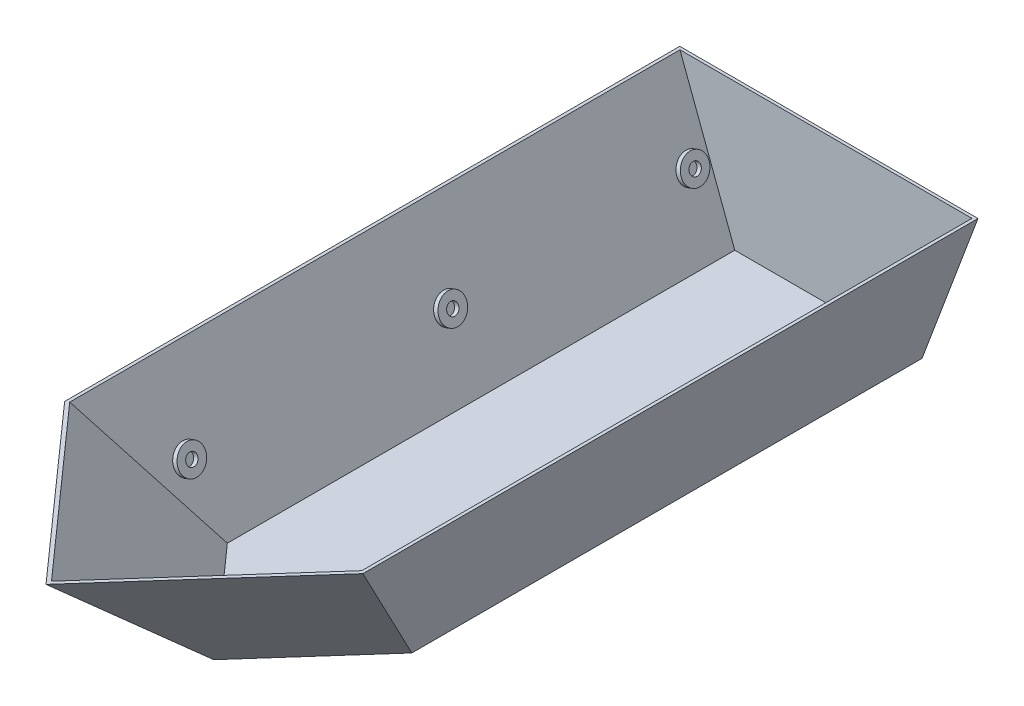
SolidWorks part; units mm, degrees
ref_plane "Front Plane" through (0, 0, 0) normal (0, 0, 1) x (1, 0, 0)
ref_plane "Top Plane" through (0, 0, 0) normal (0, 1, 0) x (1, 0, 0)
ref_plane "Right Plane" through (0, 0, 0) normal (1, 0, 0) x (0, 0, -1)
sketch "Sketch1" plane through (0, 0, 0) normal (0, 0, 1) x (1, 0, 0)
  line L0 (0, 0) -> (508, 0)
  line L1 (0, 0) -> (0, 406.4) construction
  line L2 (0, 406.4) -> (-152.4, 406.4) construction
  line L3 (-152.4, 406.4) -> (0, 0)
  line L4 (508, 0) -> (660.4, 0) construction
  line L5 (508, 0) -> (660.4, 406.4)
  line L6 (660.4, 406.4) -> (-152.4, 406.4)
  line L7 (660.4, 0) -> (660.4, 406.4) construction
  dimension "D1" = 508
  dimension "D2" = 406.4
  dimension "D3" = 152.4
  dimension "D4" = 152.4
extrude "Boss-Extrude1" add sketch "Sketch1" along normal blind 2133.6
sketch "Sketch4" plane through (0, 406.4, 0) normal (0, 1, 0) x (1, 0, 0)
  line L4 (660.4, -2133.6) -> (660.4, -1676.4) construction
  line L5 (660.4, -2133.6) -> (660.4, 0) construction
  line L6 (660.4, -1676.4) -> (-152.4, -1676.4) construction
  line L7 (-152.4, -2133.6) -> (-152.4, 0) construction
  line L11 (-152.4, -1676.4) -> (254, -2133.6) construction
  line L12 (660.4, -2133.6) -> (-152.4, -2133.6) construction
  line L13 (254, -2133.6) -> (660.4, -1676.4) construction
  dimension "D1" = 457.2
ref_plane "Plane2" through (254, 0, 0) normal (1, 0, 0) x (0, 0, -1)
sketch "Sketch13" plane through (254, 0, 0) normal (1, 0, 0) x (0, 0, -1)
  line L0 (-2133.6, 0) -> (-3174.6486, 0)
  line L1 (-2133.6, 406.4) -> (-1676.4, 0)
  line L2 (-2133.6, 406.4) -> (-1676.4, 406.4) construction
  line L3 (-2133.6, 0) -> (0, 0) construction
  line L5 (-2133.6, 0) -> (-1676.4, 0)
  line L6 (-3174.6486, 0) -> (-3174.6486, 406.4)
  line L7 (-3174.6486, 406.4) -> (-2133.6, 406.4)
  dimension "D1" = 457.2
extrude "Cut-Extrude2" cut sketch "Sketch13" along direction (0.6644, 0, 0.7474) on the side against the normal through all and the other way through all contours L7 L1 L5 L0 L6
mirror "Mirror1" about plane through (254, 0, 0) normal (1, 0, 0) of "Cut-Extrude2"
shell "Shell1" thickness 7.9375
sketch "Sketch14" plane through (437.9378, -164.2267, 0) normal (-0.9363, 0.3511, 0) x (0, 0, 1)
  line L1 (7.9375, 183.8714) -> (7.9375, 609.4295) construction
  line L2 (1671.0211, 609.4295) -> (7.9375, 609.4295) construction
  circle A0 centre (719.1375, 380.8295) radius 15.875
  circle A1 centre (58.7375, 380.8295) radius 15.875
  circle A2 centre (1430.3375, 380.8295) radius 15.875
  circle A3 centre (58.7375, 380.8295) radius 38.1
  circle A4 centre (719.1375, 380.8295) radius 38.1
  circle A5 centre (1430.3375, 380.8295) radius 38.1
  dimension "D1" = 31.75
  dimension "D2" = 711.2
  dimension "D3" = 228.6
  dimension "D4" = 31.75
  dimension "D5" = 50.8
  dimension "D6" = 228.6
  dimension "D7" = 31.75
  dimension "D8" = 228.6
  dimension "D9" = 1422.4
  dimension "D10" = 76.2
  dimension "D11" = 76.2
  dimension "D12" = 76.2
extrude "Boss-Extrude2" add sketch "Sketch14" along normal blind 12.7
mirror "Mirror2" about plane through (254, 0, 0) normal (1, 0, 0) of "Boss-Extrude2"
